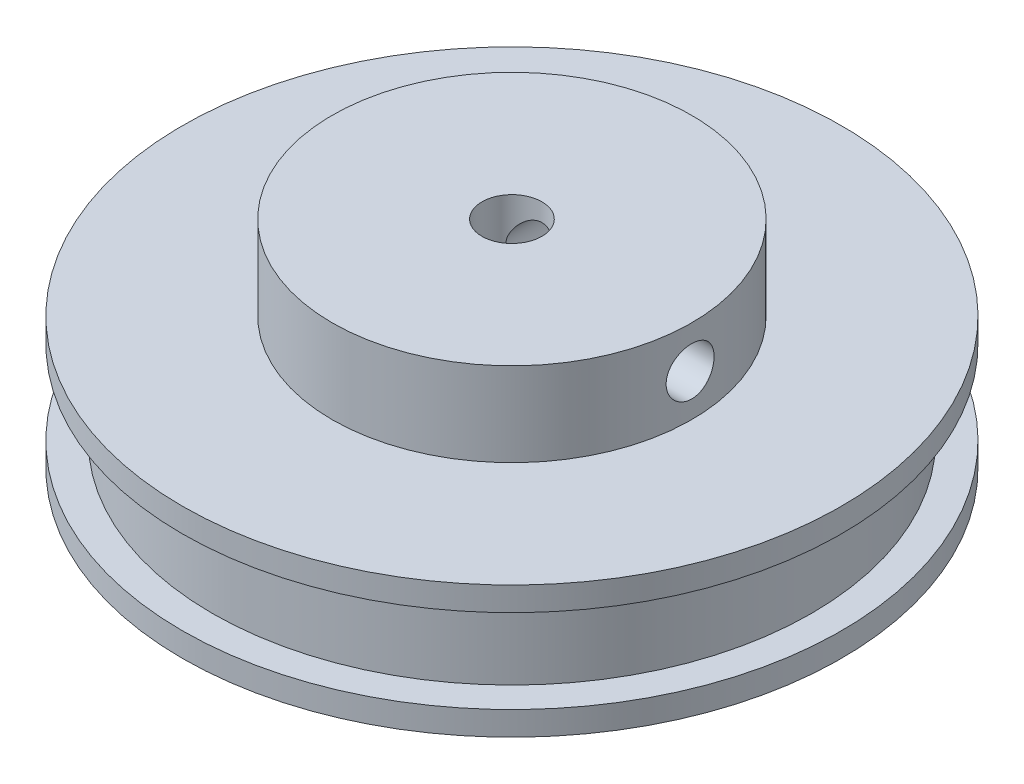
SolidWorks part; units mm, degrees
ref_plane "Front Plane" through (0, 0, 0) normal (0, 0, 1) x (1, 0, 0)
ref_plane "Top Plane" through (0, 0, 0) normal (0, 1, 0) x (1, 0, 0)
ref_plane "Right Plane" through (0, 0, 0) normal (1, 0, 0) x (0, 0, -1)
sketch "Sketch1" plane through (0, 0, 0) normal (0, 1, 0) x (1, 0, 0)
  circle A0 centre (0, 0) radius 27.5
  dimension "D1" = 55
extrude "Boss-Extrude1" add sketch "Sketch1" along normal blind 2
sketch "Sketch2" plane through (0, 2, 0) normal (0, 1, 0) x (1, 0, 0)
  circle A0 centre (0, 0) radius 25
  dimension "D1" = 50
extrude "Boss-Extrude2" add sketch "Sketch2" along normal blind 7
sketch "Sketch3" plane through (0, 9, 0) normal (0, 1, 0) x (1, 0, 0)
  circle A0 centre (0, 0) radius 27.5
  dimension "D1" = 55
extrude "Boss-Extrude3" add sketch "Sketch3" along normal blind 2
sketch "Sketch4" plane through (0, 11, 0) normal (0, 1, 0) x (1, 0, 0)
  circle A0 centre (0, 0) radius 15
  dimension "D1" = 30
extrude "Boss-Extrude4" add sketch "Sketch4" along normal blind 7
sketch "Sketch5" plane through (0, 18, 0) normal (0, 1, 0) x (1, 0, 0)
  circle A0 centre (0, 0) radius 2.5
  dimension "D1" = 5
extrude "Cut-Extrude1" cut sketch "Sketch5" against normal through all
sketch "Sketch6" plane through (0, 0, 0) normal (0, 0, 1) x (1, 0, 0)
  line L0 (15, 18) -> (-15, 18) construction
  circle A0 centre (0, 14.5) radius 2
  point P4 (0, 0)
  dimension "D1" = 4
  dimension "D2" = 3.5
extrude "Cut-Extrude2" cut sketch "Sketch6" against normal through all
pattern_circular "CirPattern1" count 2 every 90 about axis through (0, 18, 0) along (0, -1, 0) of "Cut-Extrude2"
